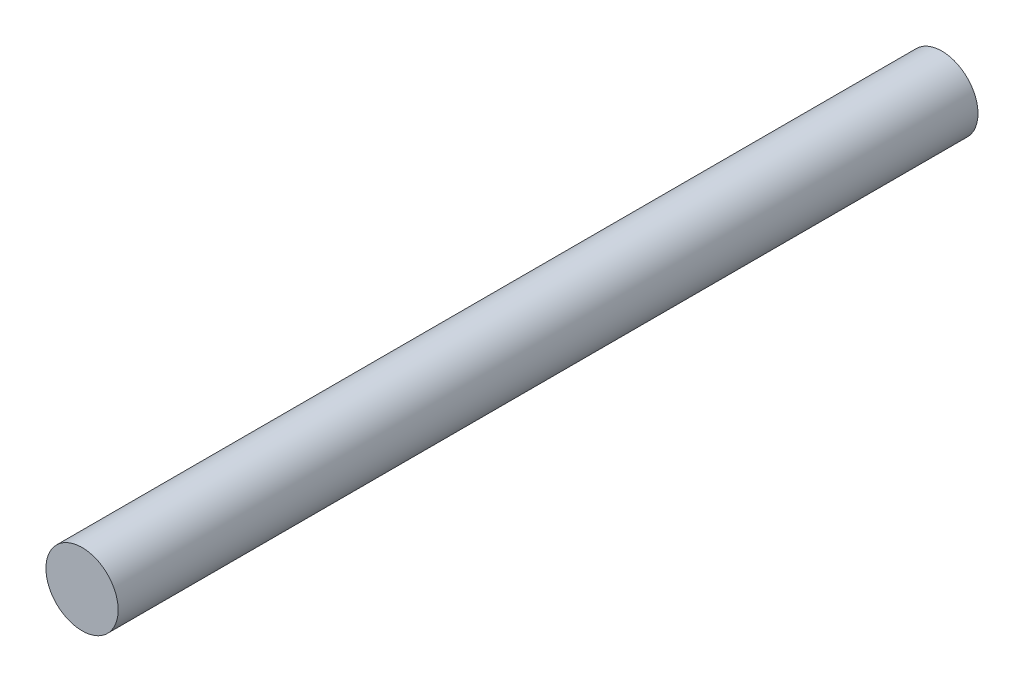
SolidWorks part; units mm, degrees
ref_plane "Front Plane" through (0, 0, 0) normal (0, 0, 1) x (1, 0, 0)
ref_plane "Top Plane" through (0, 0, 0) normal (0, 1, 0) x (1, 0, 0)
ref_plane "Right Plane" through (0, 0, 0) normal (1, 0, 0) x (0, 0, -1)
sketch "Sketch1" plane through (0, 0, 0) normal (0, 0, 1) x (1, 0, 0)
  circle A0 centre (0, 0) radius 1.27
extrude "Extrude1" add sketch "Sketch1" along normal blind 30.226
sketch "Sketch2" plane through (0, 0, 30.226) normal (0, 0, 1) x (1, 0, 0)
  line L0 (0, 0) -> (0, 1.27) construction
  circle A0 centre (0, 0) radius 1.27 construction
